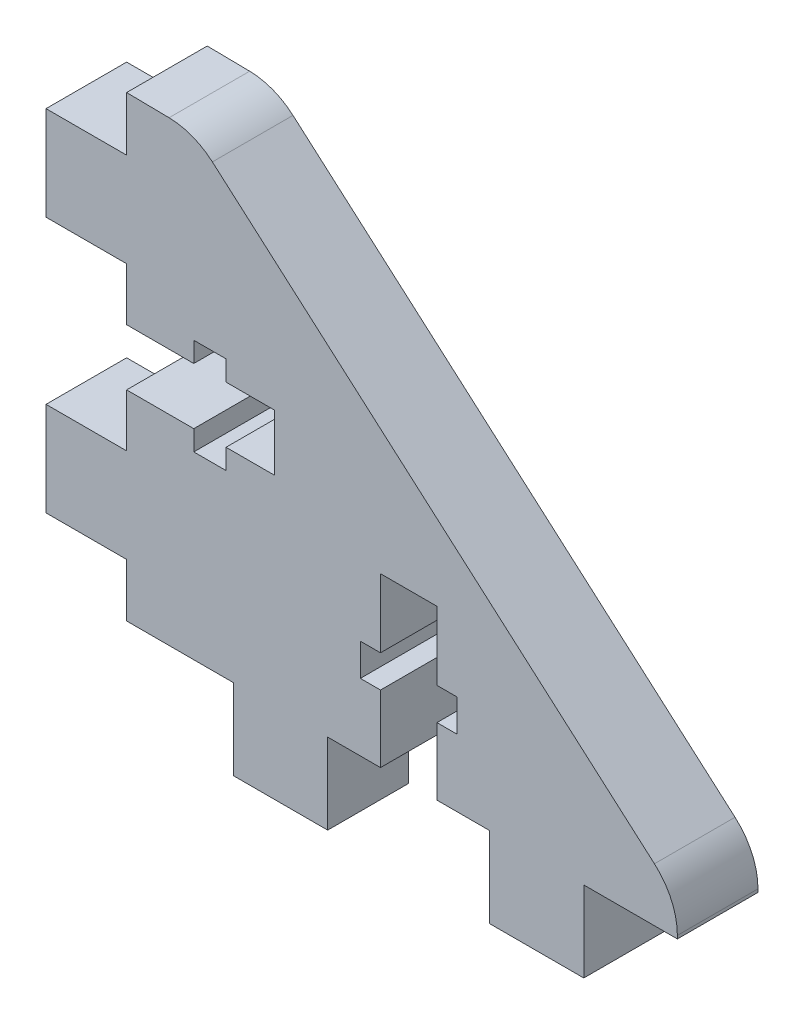
SolidWorks part; units mm, degrees
material "Клен"
ref_plane "Спереди" through (0, 0, 0) normal (0, 0, 1) x (1, 0, 0)
ref_plane "Сверху" through (0, 0, 0) normal (0, 1, 0) x (1, 0, 0)
ref_plane "Справа" through (0, 0, 0) normal (1, 0, 0) x (0, 0, -1)
sketch "Эскиз1" plane through (0, 0, 0) normal (0, 0, 1) x (1, 0, 0)
  line L3 (47, 6.0784) -> (6, 6.0784)
  line L5 (57, 6.0784) -> (-11, 6.0784) construction
  line L6 (47, 6.0784) -> (47, 6.3095)
  line L8 (6, 40.1476) -> (6, 6.0784)
  line L9 (6, 40.1476) -> (9.1609, 40.1039)
  line L12 (12.3842, 38.8672) -> (45.2925, 10.0724)
  arc A2 (9.1609, 40.1039) -> (12.3842, 38.8672) centre (9.0917, 35.1043) cw
  arc A3 (45.2925, 10.0724) -> (47, 6.3095) centre (42, 6.3095) cw
  point P10 (11, 40.0784)
  point P13 (47, 8.5784)
  dimension "D1" = 5
  dimension "D2" = 5
  dimension "D5" = 5
  dimension "D3" = 2.5
  dimension "D4" = 41
extrude "Бобышка-Вытянуть1" add sketch "Эскиз1" against normal blind 6
sketch "Эскиз23" plane through (27, 56.0784, -6) normal (0, 0, -1) x (1, 0, 0)
  line L1 (-13.0318, 50) -> (-6.0318, 50)
  line L2 (-13.0318, 50) -> (-13.0318, 56)
  line L3 (-13.0318, 56) -> (-6.0318, 56)
  line L4 (-6.0318, 50) -> (-6.0318, 56)
  line L5 (13, 56) -> (-13, 56) construction
  line L6 (0, 53.4074) -> (0, -162.0434) construction
  line L7 (13.0318, 50) -> (6.0318, 50)
  line L8 (6.0318, 50) -> (6.0318, 56)
  line L9 (13.0318, 56) -> (6.0318, 56)
  line L10 (13.0318, 50) -> (13.0318, 56)
  dimension "D1" = 7
extrude "Бобышка-Вытянуть23" add sketch "Эскиз23" against normal blind 6
sketch "Эскиз31" plane through (27, 56.0784, -6) normal (0, 0, -1) x (1, 0, 0)
  line L3 (-2.1, 45) -> (-3.6, 45)
  line L4 (-3.6, 45) -> (-3.6, 42.6)
  line L5 (-3.6, 42.6) -> (-2.1, 42.6)
  line L8 (0, 53.4074) -> (0, -162.0434) construction
  line L11 (3.6, 42.6) -> (2.1, 42.6)
  line L12 (3.6, 45) -> (3.6, 42.6)
  line L13 (2.1, 45) -> (3.6, 45)
  line L16 (-2.1, 45) -> (-2.1, 50)
  line L17 (-2.1, 50) -> (2.1, 50)
  line L18 (2.1, 50) -> (2.1, 45)
  line L19 (2.1, 42.6) -> (2.1, 37.5)
  line L20 (2.1, 37.5) -> (-2.1, 37.5)
  line L21 (-2.1, 37.5) -> (-2.1, 42.6)
  point P15 (0, 43.65)
  point P20 (0, 50)
  dimension "D2" = 7.2
  dimension "D3" = 2.4
  dimension "D4" = 4.2
extrude "Вырез-Вытянуть11" cut sketch "Эскиз31" against normal through all
other "Авто-элемент1<DIN 7991-1>"
sketch "Эскиз2" plane through (56, 23.0784, -6) normal (0, 0, -1) x (0, -1, 0)
  line L1 (-13.0318, 50) -> (-6.0318, 50)
  line L2 (-13.0318, 50) -> (-13.0318, 56)
  line L3 (-13.0318, 56) -> (-6.0318, 56)
  line L4 (-6.0318, 50) -> (-6.0318, 56)
  line L5 (13, 56) -> (-13, 56) construction
  line L6 (0, 53.4074) -> (0, -162.0434) construction
  line L7 (13.0318, 50) -> (6.0318, 50)
  line L8 (6.0318, 50) -> (6.0318, 56)
  line L9 (13.0318, 56) -> (6.0318, 56)
  line L10 (13.0318, 50) -> (13.0318, 56)
  dimension "D1" = 7
extrude "Бобышка-Вытянуть2" add sketch "Эскиз2" against normal blind 6
sketch "Эскиз3" plane through (56, 23.0784, -6) normal (0, 0, -1) x (0, -1, 0)
  line L3 (-2.1, 45) -> (-3.6, 45)
  line L4 (-3.6, 45) -> (-3.6, 42.6)
  line L5 (-3.6, 42.6) -> (-2.1, 42.6)
  line L8 (0, 53.4074) -> (0, -162.0434) construction
  line L11 (3.6, 42.6) -> (2.1, 42.6)
  line L12 (3.6, 45) -> (3.6, 42.6)
  line L13 (2.1, 45) -> (3.6, 45)
  line L16 (-2.1, 45) -> (-2.1, 50)
  line L17 (-2.1, 50) -> (2.1, 50)
  line L18 (2.1, 50) -> (2.1, 45)
  line L19 (2.1, 42.6) -> (2.1, 39)
  line L20 (2.1, 39) -> (-2.1, 39)
  line L21 (-2.1, 39) -> (-2.1, 42.6)
  point P15 (0, 43.65)
  point P20 (0, 50)
  dimension "D2" = 7.2
  dimension "D3" = 2.4
  dimension "D4" = 4.2
extrude "Вырез-Вытянуть1" cut sketch "Эскиз3" against normal through all
other "Авто-элемент5<DIN967-8>"
sketch "Эскиз24" plane through (56, 23.0784, 0) normal (0, 0, 1) x (0, 1, 0)
  line L1 (-13.0318, 50) -> (-6.0318, 50)
  line L2 (-13.0318, 50) -> (-13.0318, 56)
  line L3 (-13.0318, 56) -> (-6.0318, 56)
  line L4 (-6.0318, 50) -> (-6.0318, 56)
  line L5 (13, 56) -> (-13, 56) construction
  line L6 (0, 53.4074) -> (0, -162.0434) construction
  line L7 (13.0318, 50) -> (6.0318, 50)
  line L8 (6.0318, 50) -> (6.0318, 56)
  line L9 (13.0318, 56) -> (6.0318, 56)
  line L10 (13.0318, 50) -> (13.0318, 56)
  dimension "D1" = 7
extrude "Бобышка-Вытянуть24" add sketch "Эскиз24" against normal blind 6
other "Авто-элемент6<DIN967-9>"
sketch "Эскиз25" plane through (27, 56.0784, -6) normal (0, 0, -1) x (1, 0, 0)
  line L1 (-13.0318, 50) -> (-6.0318, 50)
  line L2 (-13.0318, 50) -> (-13.0318, 56)
  line L3 (-13.0318, 56) -> (-6.0318, 56)
  line L4 (-6.0318, 50) -> (-6.0318, 56)
  line L5 (13, 56) -> (-13, 56) construction
  line L6 (0, 53.4074) -> (0, -162.0434) construction
  line L7 (13.0318, 50) -> (6.0318, 50)
  line L8 (6.0318, 50) -> (6.0318, 56)
  line L9 (13.0318, 56) -> (6.0318, 56)
  line L10 (13.0318, 50) -> (13.0318, 56)
  dimension "D1" = 7
extrude "Бобышка-Вытянуть26" add sketch "Эскиз25" against normal blind 6
other "Авто-элемент1<DIN 7991-1>"
